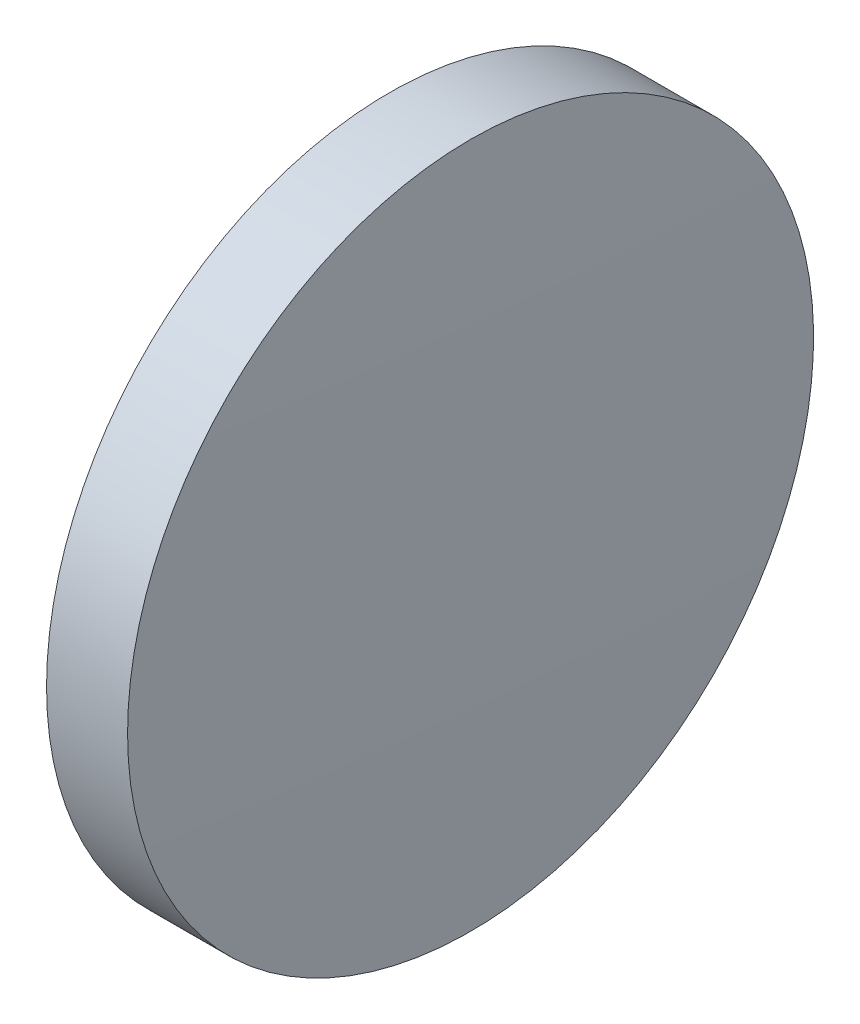
SolidWorks part; units mm, degrees
ref_plane "前视基准面" through (0, 0, 0) normal (0, 0, 1) x (1, 0, 0)
ref_plane "上视基准面" through (0, 0, 0) normal (0, 1, 0) x (1, 0, 0)
ref_plane "右视基准面" through (0, 0, 0) normal (1, 0, 0) x (0, 0, -1)
sketch "草图1" plane through (0, 0, 0) normal (0, 0, 1) x (1, 0, 0)
  line L0 (110.1654, 65.2336) -> (128.9614, 65.2336) construction
  line L1 (115.7736, 65.2336) -> (115.7736, 77.9336)
  line L2 (115.7736, 77.9336) -> (118.7739, 77.9336)
  line L3 (118.9496, 65.2336) -> (115.7736, 65.2336)
  arc A0 (118.9496, 65.2336) -> (118.7739, 77.9336) centre (-340.0504, 65.2336) ccw
  dimension "D1" = 459
revolve "旋转1" add sketch "草图1" angle 360 about L0
